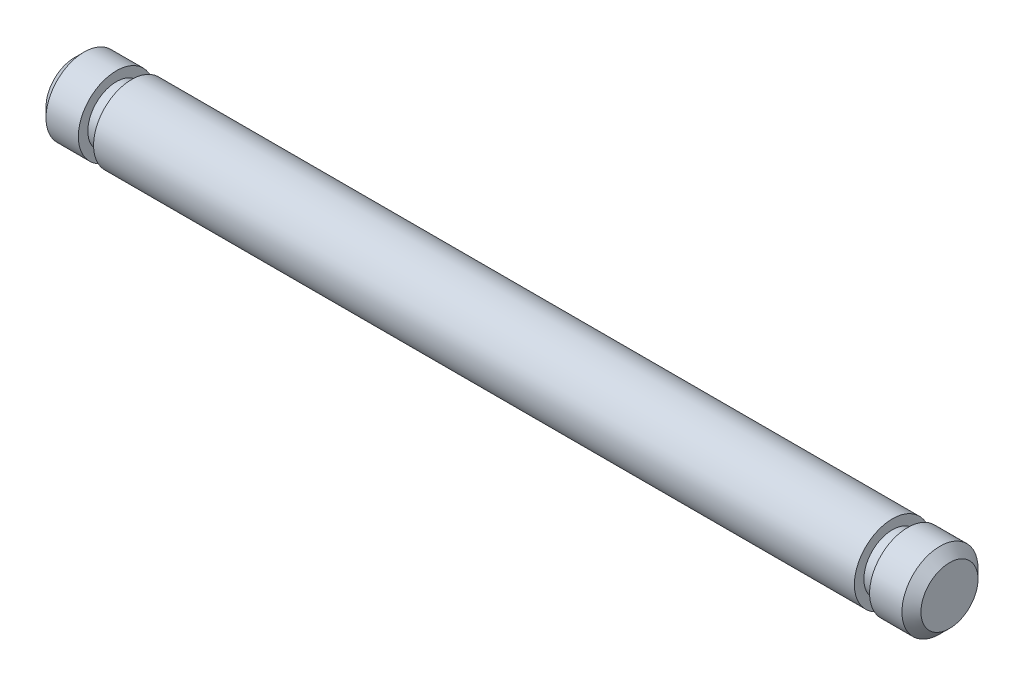
SolidWorks part; units mm, degrees
ref_plane "Front Plane" through (0, 0, 0) normal (0, 0, 1) x (1, 0, 0)
ref_plane "Top Plane" through (0, 0, 0) normal (0, 1, 0) x (1, 0, 0)
ref_plane "Right Plane" through (0, 0, 0) normal (1, 0, 0) x (0, 0, -1)
sketch "Sketch1" plane through (0, 0, 0) normal (1, 0, 0) x (0, 0, -1)
  circle A0 centre (0, 0) radius 2
extrude "Boss-Extrude1" add sketch "Sketch1" along normal blind 46
chamfer "Chamfer1" distance 0.5 angle 45 2 edges at (0, 0, -2) (46, 0, -2)
sketch "Sketch2" plane through (46, 0, 0) normal (1, 0, 0) x (0, 0, -1)
  circle A1 centre (0, 0) radius 1.5
  circle A2 centre (0, 0) radius 1.5
  circle A3 centre (0, 0) radius 2 construction
  circle A4 centre (0, 0) radius 2
  dimension "D1" = 0
extrude "Cut-Extrude1" cut sketch "Sketch2" along normal blind 0.8 from offset 3 offset against normal yes
sketch "Sketch3" plane through (0, 0, 0) normal (-1, 0, 0) x (0, 0, 1)
  circle A0 centre (0, 0) radius 2 construction
  circle A1 centre (0, 0) radius 1.5
  circle A2 centre (0, 0) radius 1.5
  circle A3 centre (0, 0) radius 2
  dimension "D1" = 0
extrude "Cut-Extrude2" cut sketch "Sketch3" along normal blind 0.8 from offset 3
